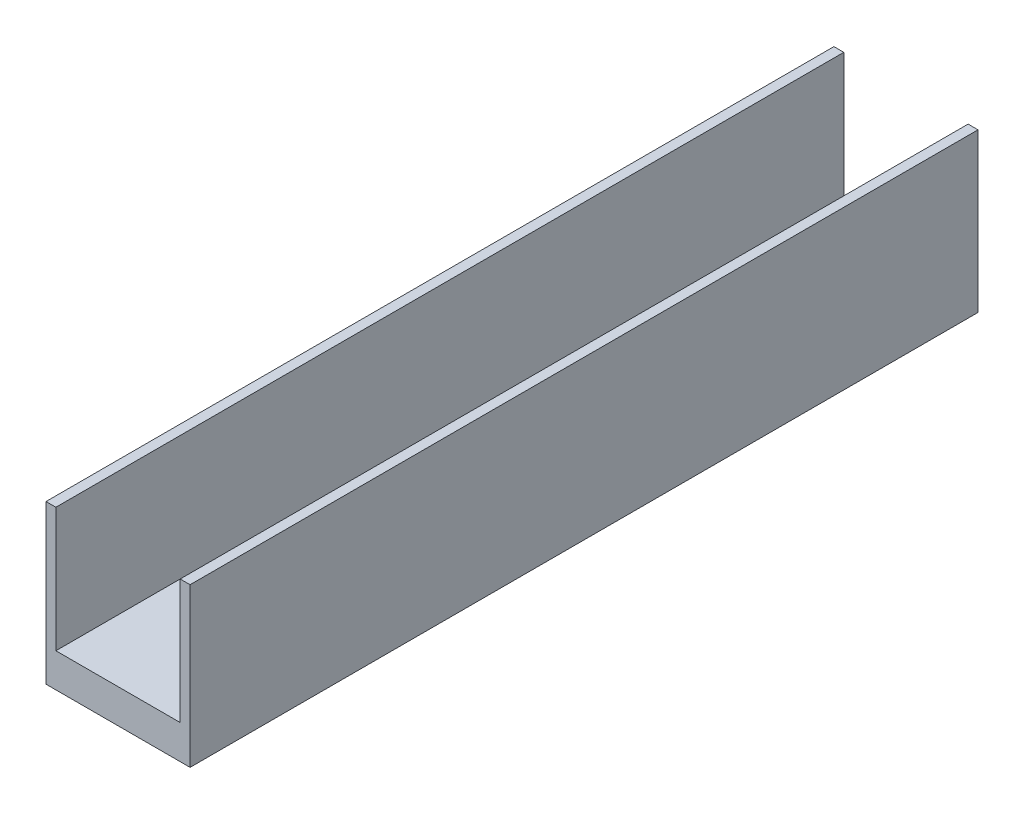
SolidWorks part; units mm, degrees
ref_plane "Front Plane" through (0, 0, 0) normal (0, 0, 1) x (1, 0, 0)
ref_plane "Top Plane" through (0, 0, 0) normal (0, 1, 0) x (1, 0, 0)
ref_plane "Right Plane" through (0, 0, 0) normal (1, 0, 0) x (0, 0, -1)
sketch "Sketch1" plane through (0, 0, 0) normal (0, 0, 1) x (1, 0, 0)
  line L0 (0, 0) -> (0, 88.9)
  line L1 (0, 88.9) -> (5.5562, 88.9)
  line L2 (5.5562, 88.9) -> (5.5562, 19.05)
  line L3 (5.5562, 19.05) -> (75.4062, 19.05)
  line L4 (75.4062, 19.05) -> (75.4062, 88.9)
  line L5 (75.4062, 88.9) -> (80.9625, 88.9)
  line L6 (80.9625, 88.9) -> (80.9625, 0)
  line L7 (80.9625, 0) -> (0, 0)
  dimension "D1" = 19.05
  dimension "D2" = 80.9625
  dimension "D3" = 69.85
  dimension "D4" = 88.9
extrude "Boss-Extrude1" add sketch "Sketch1" along normal blind 442.7347
